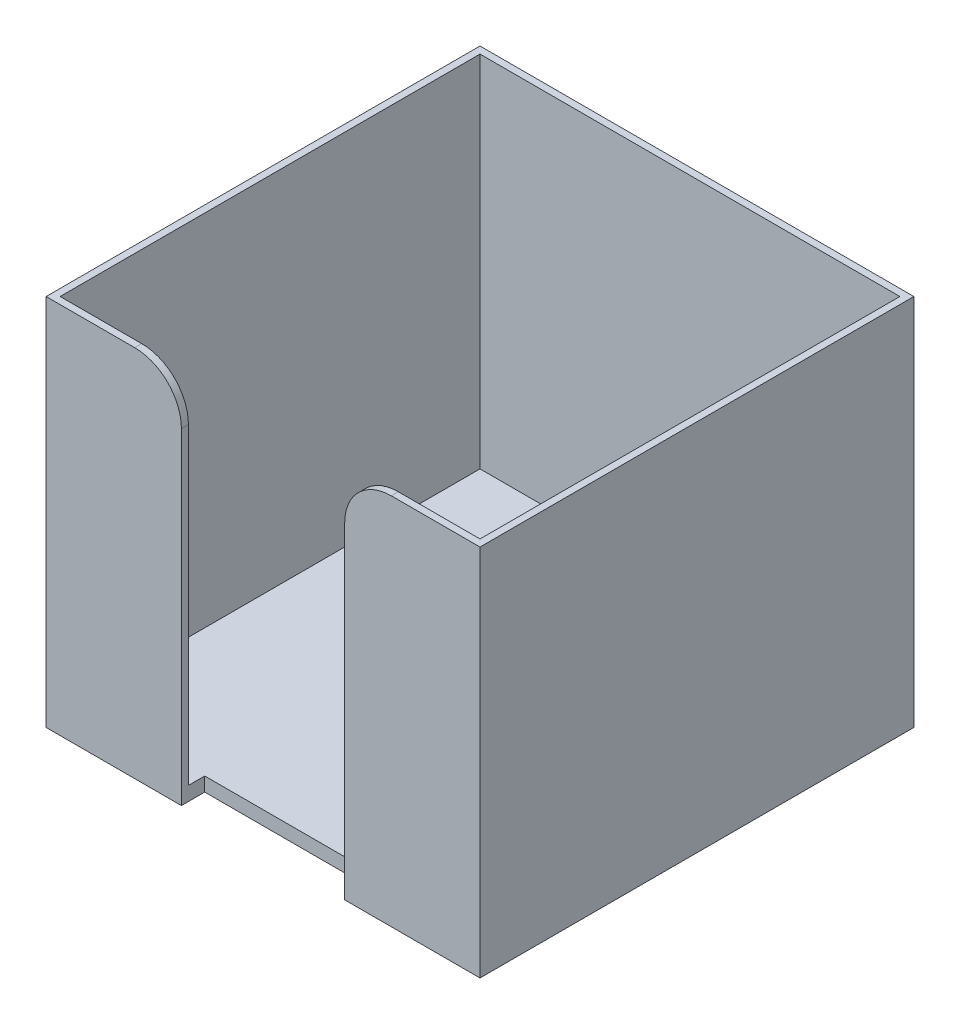
SolidWorks part; units mm, degrees
ref_plane "Front Plane" through (0, 0, 0) normal (0, 0, 1) x (1, 0, 0)
ref_plane "Top Plane" through (0, 0, 0) normal (0, 1, 0) x (1, 0, 0)
ref_plane "Right Plane" through (0, 0, 0) normal (1, 0, 0) x (0, 0, -1)
sketch "Sketch1" plane through (0, 0, 0) normal (0, 1, 0) x (1, 0, 0)
  line L1 (-46.5, 46.5) -> (46.5, 46.5)
  line L2 (-46.5, 46.5) -> (-46.5, -46.5)
  line L3 (-46.5, -46.5) -> (46.5, -46.5)
  line L4 (46.5, 46.5) -> (46.5, -46.5)
  line L5 (-46.5, 46.5) -> (46.5, -46.5) construction
  line L6 (-46.5, -46.5) -> (46.5, 46.5) construction
  point P0 (0, 0)
  dimension "D1" = 93
  dimension "D2" = 93
extrude "Boss-Extrude1" add sketch "Sketch1" along normal blind 80 contours L2 L1 L4 L3
sketch "Sketch3" plane through (0, 80, 0) normal (0, 1, 0) x (1, 0, 0)
  line L1 (-45, 45) -> (45, 45)
  line L2 (-45, 45) -> (-45, -45)
  line L3 (-45, -45) -> (45, -45)
  line L4 (45, 45) -> (45, -45)
  line L5 (-45, 45) -> (45, -45) construction
  line L6 (-45, -45) -> (45, 45) construction
  point P0 (0, 0)
  dimension "D1" = 90
  dimension "D2" = 90
extrude "Cut-Extrude1" cut sketch "Sketch3" against normal blind 77
sketch "Sketch4" plane through (0, 0, 46.5) normal (0, 0, 1) x (1, 0, 0)
  line L0 (-46.5, 80) -> (46.5, 80) construction
  line L1 (-17.5, 80) -> (17.5, 80)
  line L2 (-17.5, 80) -> (-17.5, 0)
  line L3 (-17.5, 0) -> (17.5, 0)
  line L4 (17.5, 80) -> (17.5, 0)
  line L5 (-46.5, 0) -> (46.5, 0) construction
  line L6 (46.5, 80) -> (46.5, 0) construction
  dimension "D1" = 35
  dimension "D2" = 29
extrude "Cut-Extrude2" cut sketch "Sketch4" against normal blind 5
fillet "Fillet1" radius 10 2 edges at (17.5, 80, 45.75) (-17.5, 80, 45.75)
